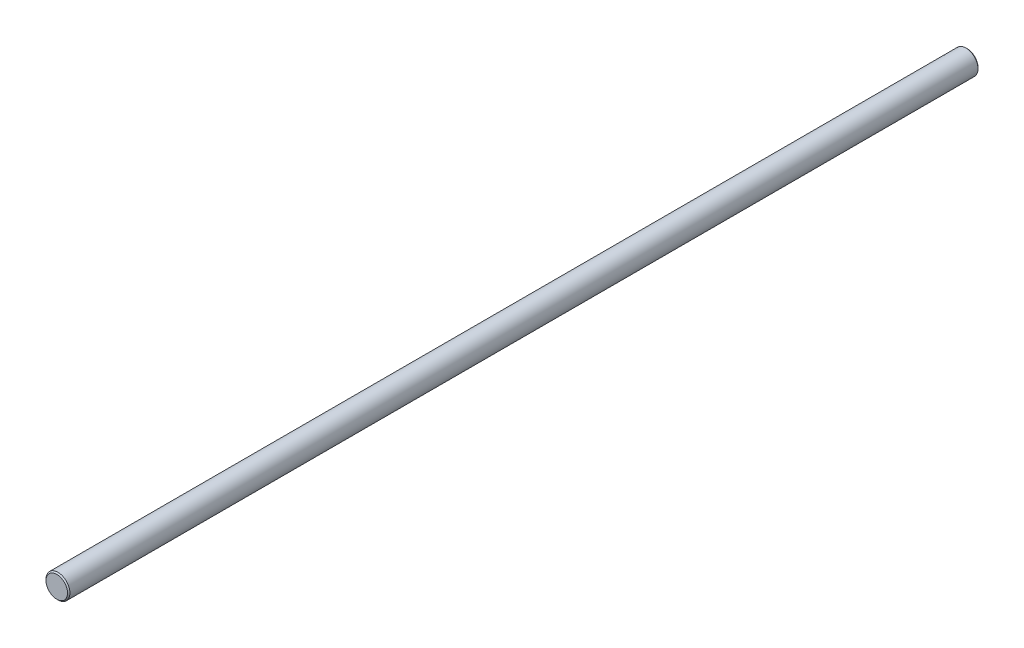
SolidWorks part; units mm, degrees
material "AISI 304"
ref_plane "Front Plane" through (0, 0, 0) normal (0, 0, 1) x (1, 0, 0)
ref_plane "Top Plane" through (0, 0, 0) normal (0, 1, 0) x (1, 0, 0)
ref_plane "Right Plane" through (0, 0, 0) normal (1, 0, 0) x (0, 0, -1)
sketch "Sketch1" plane through (0, 0, 0) normal (0, 0, 1) x (1, 0, 0)
  circle A0 centre (0, 0) radius 5
  dimension "D1" = 10
extrude "Boss-Extrude1" add sketch "Sketch1" against normal blind 380
cosmetic thread "Cosmetic Thread1"
chamfer "Chamfer1" distance 0.5 angle 45 2 edges at (5, 0, -380) (5, 0, 0)
